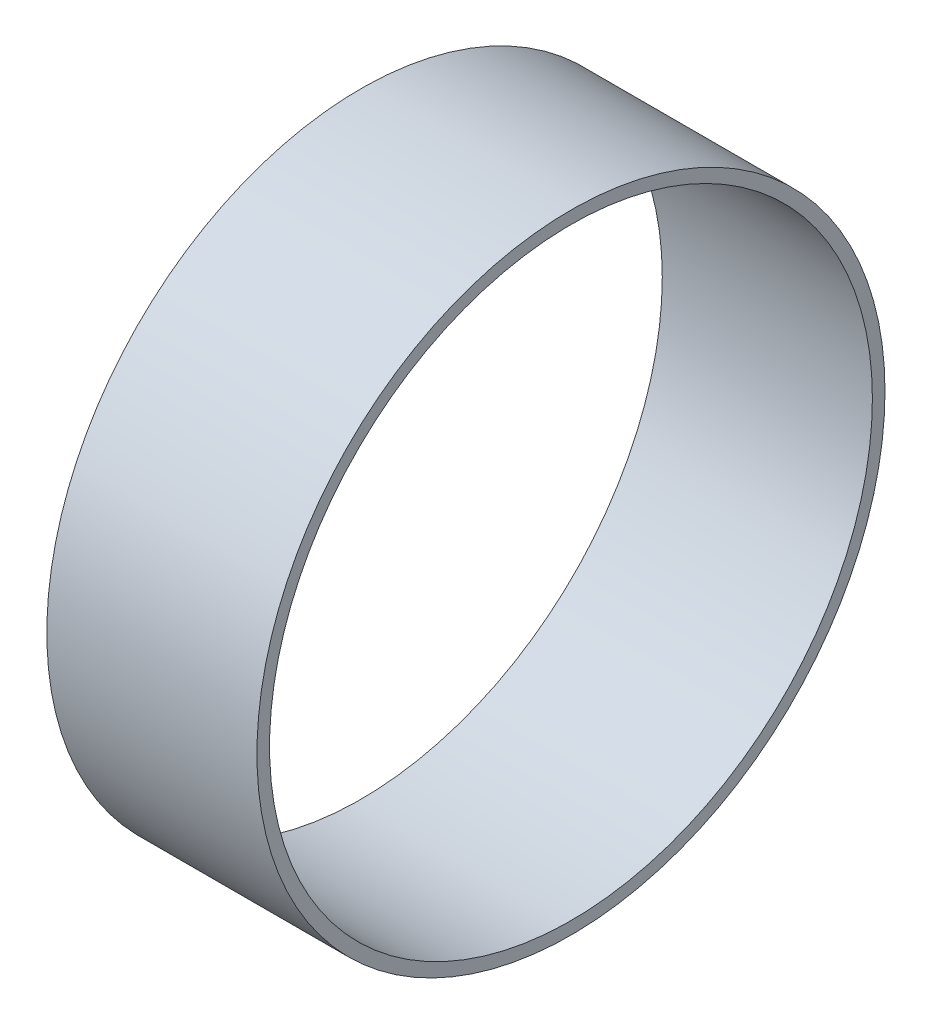
SolidWorks part; units mm, degrees
material "Wildman Fiberglass"
ref_plane "Front Plane" through (0, 0, 0) normal (0, 0, 1) x (1, 0, 0)
ref_plane "Top Plane" through (0, 0, 0) normal (0, 1, 0) x (1, 0, 0)
ref_plane "Right Plane" through (0, 0, 0) normal (1, 0, 0) x (0, 0, -1)
sketch "Sketch1" plane through (0, 0, 0) normal (1, 0, 0) x (0, 0, -1)
  circle A0 centre (0, 0) radius 28.4734
  circle A1 centre (0, 0) radius 27.3304
  dimension "D1" = 56.9468
  dimension "D2" = 54.6608
extrude "Boss-Extrude1" add sketch "Sketch1" along normal mid plane 19.05
